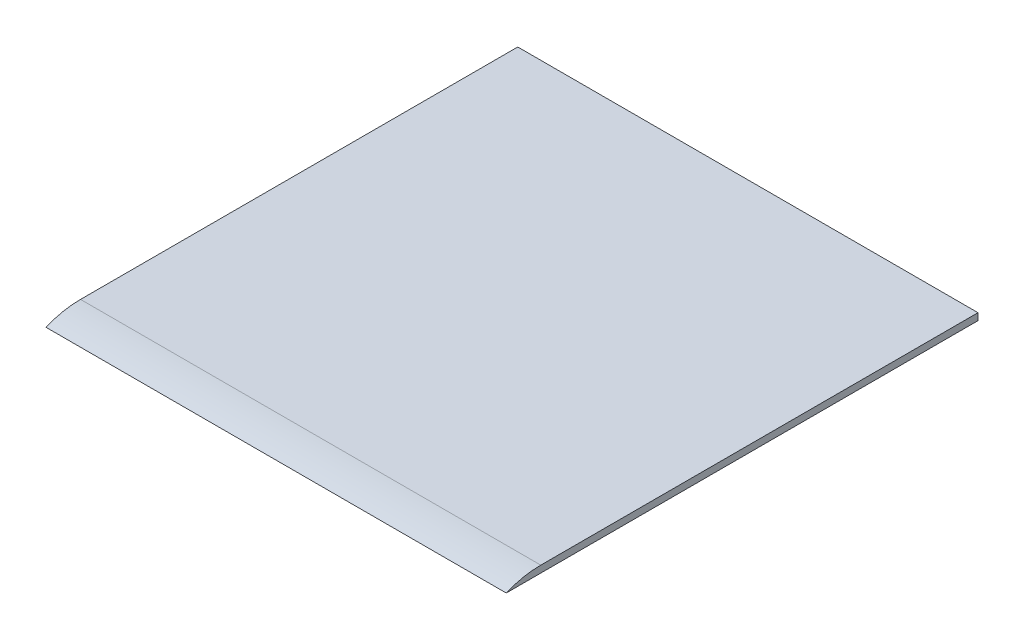
SolidWorks part; units mm, degrees
material "Aleación 1060"
ref_plane "Alzado" through (0, 0, 0) normal (0, 0, 1) x (1, 0, 0)
ref_plane "Planta" through (0, 0, 0) normal (0, 1, 0) x (1, 0, 0)
ref_plane "Vista lateral" through (0, 0, 0) normal (1, 0, 0) x (0, 0, -1)
sketch "Croquis3" plane through (0, 0, 0) normal (1, 0, 0) x (0, 0, -1)
  line L0 (102.5, 0) -> (-102.5, 0)
  line L1 (102.5, 0) -> (102.5, 3)
  line L2 (102.5, 3) -> (-87.5, 3)
  arc A0 (-87.5, 3) -> (-102.5, 0) centre (-87.5, -36) ccw
  point P4 (0, 0)
  dimension "D1" = 205
  dimension "D2" = 3
  dimension "D3" = 190
extrude "Saliente-Extruir1" add sketch "Croquis3" along normal mid plane 200
